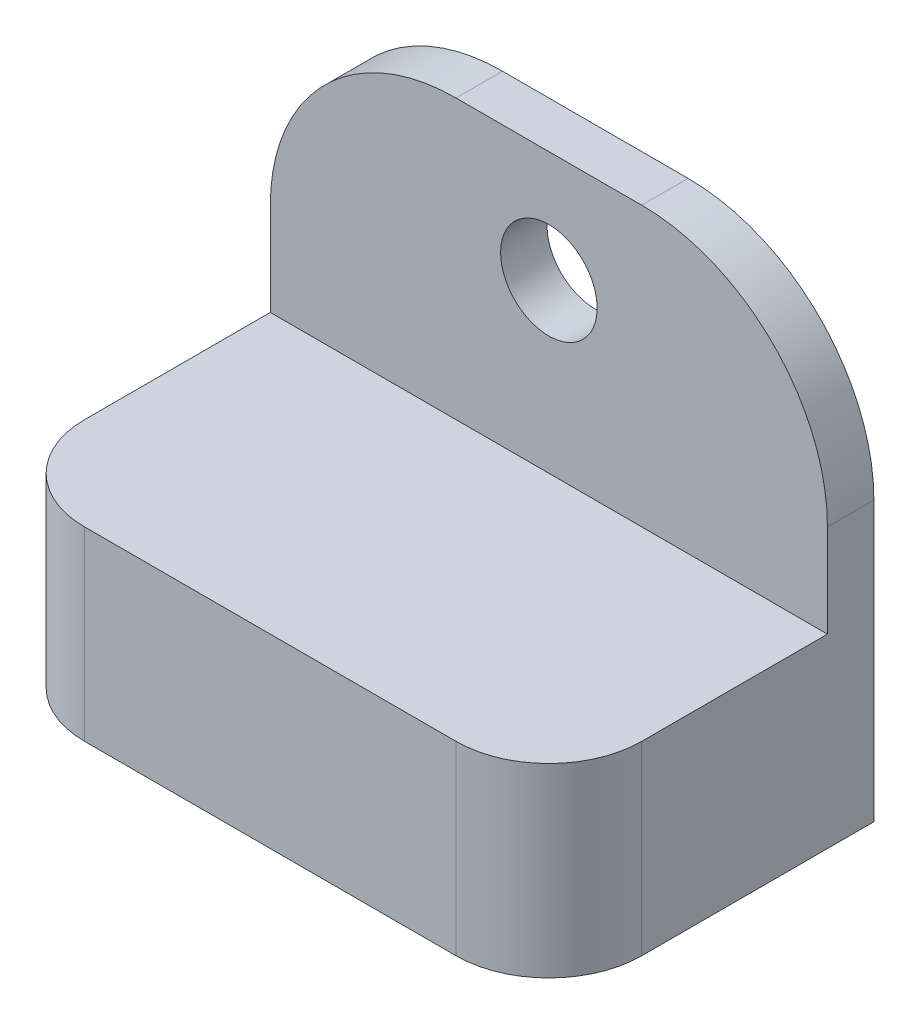
SolidWorks part; units mm, degrees
ref_plane "Front Plane" through (0, 0, 0) normal (0, 0, 1) x (1, 0, 0)
ref_plane "Top Plane" through (0, 0, 0) normal (0, 1, 0) x (1, 0, 0)
ref_plane "Right Plane" through (0, 0, 0) normal (1, 0, 0) x (0, 0, -1)
sketch "Sketch1" plane through (0, 0, 0) normal (1, 0, 0) x (0, 0, -1)
  line L0 (0, 0) -> (-22.225, 0)
  line L1 (-22.225, 0) -> (-22.225, 12.7)
  line L2 (-22.225, 12.7) -> (-3.175, 12.7)
  line L3 (-3.175, 12.7) -> (-3.175, 31.75)
  line L4 (-3.175, 31.75) -> (0, 31.75)
  line L5 (0, 31.75) -> (0, 0)
  dimension "D1" = 12.7
  dimension "D2" = 19.05
  dimension "D3" = 3.175
  dimension "D4" = 19.05
extrude "Boss-Extrude1" add sketch "Sketch1" along normal blind 38.1
sketch "Sketch3" plane through (0, 0, 0) normal (0, 0, -1) x (-1, 0, 0)
  line L0 (-38.1, 12.7) -> (0, 12.7) construction
  line L1 (-19.05, 24.13) -> (-19.05, 31.75) construction
  line L2 (-38.1, 31.75) -> (0, 31.75) construction
  circle A0 centre (-19.05, 24.13) radius 3.302
  dimension "D1" = 6.604
  dimension "D2" = 11.43
extrude "Cut-Extrude1" cut sketch "Sketch3" against normal through all
fillet "Fillet1" radius 6.35 2 edges at (38.1, 6.35, 22.225) (0, 6.35, 22.225)
fillet "Fillet2" radius 12.7 2 edges at (38.1, 31.75, 1.5875) (0, 31.75, 1.5875)
